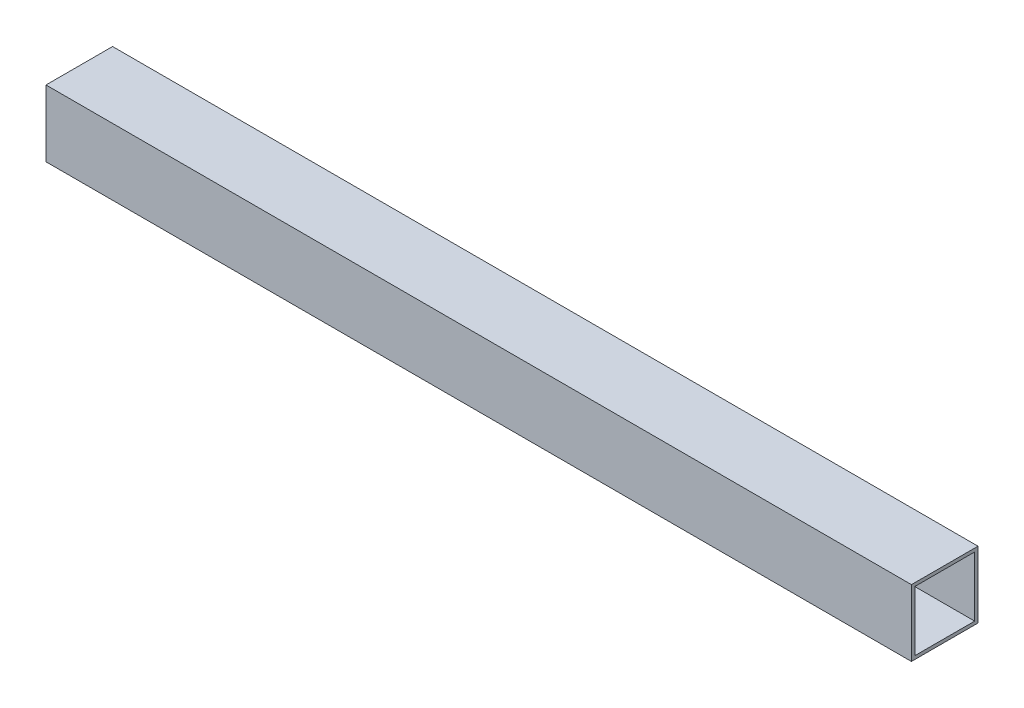
SolidWorks part; units mm, degrees
ref_plane "Alzado" through (0, 0, 0) normal (0, 0, 1) x (1, 0, 0)
ref_plane "Planta" through (0, 0, 0) normal (0, 1, 0) x (1, 0, 0)
ref_plane "Vista lateral" through (0, 0, 0) normal (1, 0, 0) x (0, 0, -1)
sketch "Croquis1" plane through (0, 0, 0) normal (1, 0, 0) x (0, 0, -1)
  line L1 (-20, -20) -> (20, -20)
  line L2 (-20, -20) -> (-20, 20)
  line L3 (-20, 20) -> (20, 20)
  line L4 (20, -20) -> (20, 20)
  line L5 (-20, -20) -> (20, 20) construction
  line L6 (-20, 20) -> (20, -20) construction
  line L7 (-18, -18) -> (18, -18)
  line L8 (-18, -18) -> (-18, 18)
  line L9 (-18, 18) -> (18, 18)
  line L10 (18, -18) -> (18, 18)
  line L11 (-18, -18) -> (18, 18) construction
  line L12 (-18, 18) -> (18, -18) construction
  point P0 (0, 0)
  point P6 (0, 0)
  dimension "D1" = 2
  dimension "D2" = 40
  dimension "D3" = 2
extrude "Saliente-Extruir1" add sketch "Croquis1" along normal blind 520
